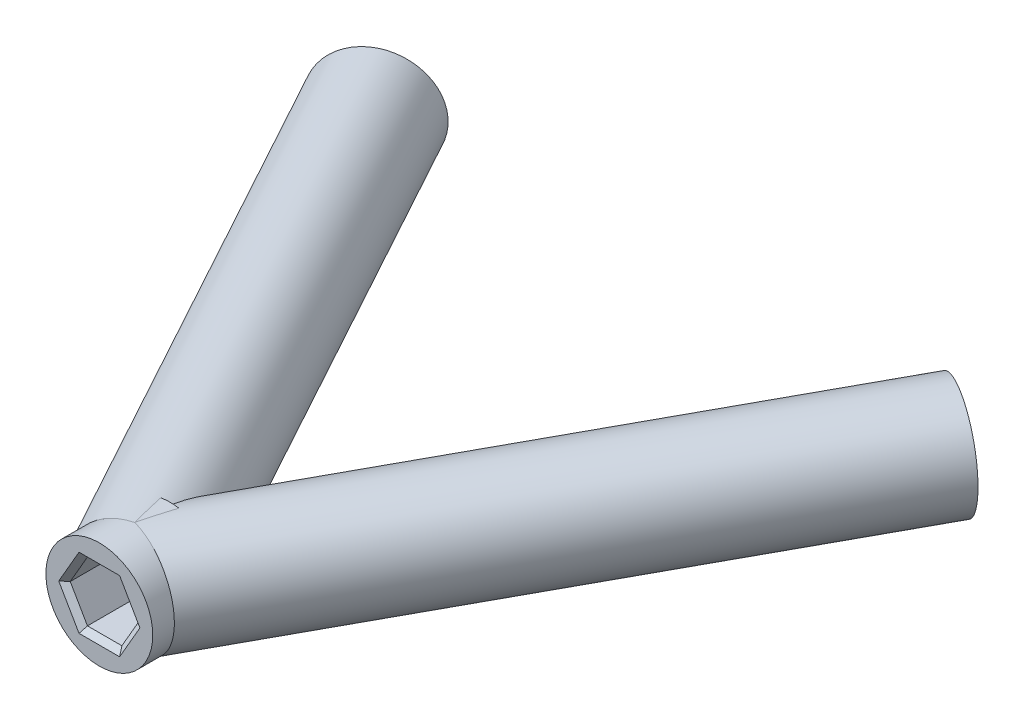
SolidWorks part; units mm, degrees
material "ABS"
ref_plane "Front Plane" through (0, 0, 0) normal (0, 0, 1) x (1, 0, 0)
ref_plane "Top Plane" through (0, 0, 0) normal (0, 1, 0) x (1, 0, 0)
ref_plane "Right Plane" through (0, 0, 0) normal (1, 0, 0) x (0, 0, -1)
sketch "Sketch1" plane through (0, 0, 0) normal (0, 1, 0) x (1, 0, 0)
  line L0 (0, 0) -> (-35.5851, 85.91) construction
  line L1 (0, 0) -> (35.5851, 85.91) construction
  line L2 (0, 0) -> (0, 85.91) construction
  line L3 (0, 17.5) -> (0, 24.1)
  line L4 (-35.5851, 85.91) -> (0, 20.8) construction
  line L5 (0, 20.8) -> (35.5851, 85.91) construction
  point P3 (0, 17.5)
  point P6 (-35.5851, 85.91)
  point P7 (35.5851, 85.91)
  point P10 (0, 20.8)
  point P13 (27.1924, 70.5538)
  point P15 (-27.1924, 70.5538)
  dimension "D1" = 45
  dimension "D2" = 85.91
  dimension "D3" = 17.5
  dimension "D4" = 17.5
  dimension "D5" = 17.5
  dimension "D6" = 6.6
  dimension "D7" = 57.317
  dimension "D8" = 92.9883
  dimension "D9" = 28.658
  dimension "D10" = 28.658
  dimension "D11" = 74.1998
  dimension "D12" = 74.1998
revolve "Revolve-Thin1" add sketch "Sketch1" angle 360 about L2 wall 5
sketch "Sketch3" plane through (0, 0, 0) normal (0, 1, 0) x (1, 0, 0)
  line L0 (-35.5851, 85.91) -> (0, 20.8) construction
  line L1 (-27.1924, 70.5538) -> (0, 20.8)
revolve "Revolve-Thin2" add sketch "Sketch3" angle 360 about L1 wall 5
sketch "Sketch4" plane through (0, 0, 0) normal (0, 1, 0) x (1, 0, 0)
  line L0 (0, 20.8) -> (35.5851, 85.91) construction
  line L1 (0, 20.8) -> (27.1924, 70.5538)
revolve "Revolve-Thin3" add sketch "Sketch4" angle 360 about L1 wall 5
sketch "Sketch5" plane through (-35.9457, 0, -65.7698) normal (-0.4796, 0, -0.8775) x (-0.8775, 0, 0.4796)
  line L0 (-9.9754, 5) -> (-9.9754, -5) construction
  line L1 (-7.0216, 1.2862) -> (-9.6124, 3.2011)
  line L2 (-9.6124, 3.2011) -> (-12.5661, 1.9149)
  line L3 (-12.5661, 1.9149) -> (-12.9291, -1.2862)
  line L4 (-12.9291, -1.2862) -> (-10.3383, -3.2011)
  line L5 (-10.3383, -3.2011) -> (-7.3846, -1.9149)
  line L6 (-7.3846, -1.9149) -> (-7.0216, 1.2862)
  line L7 (-14.9754, 0) -> (-4.9754, 0) construction
  line L8 (-9.6124, 3.2011) -> (-10.3383, -3.2011) construction
  circle A0 centre (-9.9754, 0) radius 2.79 construction
  circle A1 centre (-9.9754, 0) radius 5
  circle A2 centre (-9.9754, 0) radius 5 construction
  dimension "D2" = 5.58
  dimension "D3" = 6.469
  dimension "D1" = 0
extrude "Cut-Extrude1" cut sketch "Sketch5" against normal blind 6.6
sketch "Sketch6" plane through (0, 0, -17.5) normal (0, 0, 1) x (1, 0, 0)
  line L1 (1.6108, 2.79) -> (-1.6108, 2.79)
  line L2 (-1.6108, 2.79) -> (-3.2216, 0)
  line L3 (-3.2216, 0) -> (-1.6108, -2.79)
  line L4 (-1.6108, -2.79) -> (1.6108, -2.79)
  line L5 (1.6108, -2.79) -> (3.2216, 0)
  line L6 (3.2216, 0) -> (1.6108, 2.79)
  circle A0 centre (0, 0) radius 2.79 construction
  dimension "D1" = 5.58
extrude "Cut-Extrude2" cut sketch "Sketch6" against normal blind 6.6
sketch "Sketch7" plane through (35.9457, 0, -65.7698) normal (0.4796, 0, -0.8775) x (-0.8775, 0, -0.4796)
  line L0 (9.9754, 5) -> (9.9754, -5) construction
  line L1 (9.6124, 3.2011) -> (7.0216, 1.2862)
  line L2 (7.0216, 1.2862) -> (7.3846, -1.9149)
  line L3 (7.3846, -1.9149) -> (10.3383, -3.2011)
  line L4 (10.3383, -3.2011) -> (12.9291, -1.2862)
  line L5 (12.9291, -1.2862) -> (12.5661, 1.9149)
  line L6 (12.5661, 1.9149) -> (9.6124, 3.2011)
  line L7 (4.9754, 0) -> (14.9754, 0) construction
  line L8 (9.6124, 3.2011) -> (10.3383, -3.2011) construction
  circle A0 centre (9.9754, 0) radius 2.79 construction
  circle A1 centre (9.9754, 0) radius 5 construction
  arc A2 (11.558, -4.7429) -> (11.558, 4.7429) centre (9.9754, 0) ccw construction
  dimension "D1" = 5.58
  dimension "D2" = 6.469
extrude "Cut-Extrude3" cut sketch "Sketch7" against normal blind 6.6
chamfer "Chamfer1" distance 0.5 angle 45 18 edges at (-28.6476, 2.2437, -69.7585) (-29.625, -0.3143, -69.2243) (-28.1698, -2.558, -70.0196) (-25.7372, -2.2437, -71.3491) (-26.2149, 2.558, -71.088) (-24.7597, 0.3143, -71.8833) (2.4162, -1.395, -17.5) (2.4162, 1.395, -17.5) (0, 2.79, -17.5) (-2.4162, 1.395, -17.5) (-2.4162, -1.395, -17.5) (0, -2.79, -17.5) (28.6476, 2.2437, -69.7585) (26.2149, 2.558, -71.088) (24.7597, 0.3143, -71.8833) (25.7372, -2.2437, -71.3491) (29.625, -0.3143, -69.2243) (28.1698, -2.558, -70.0196)
